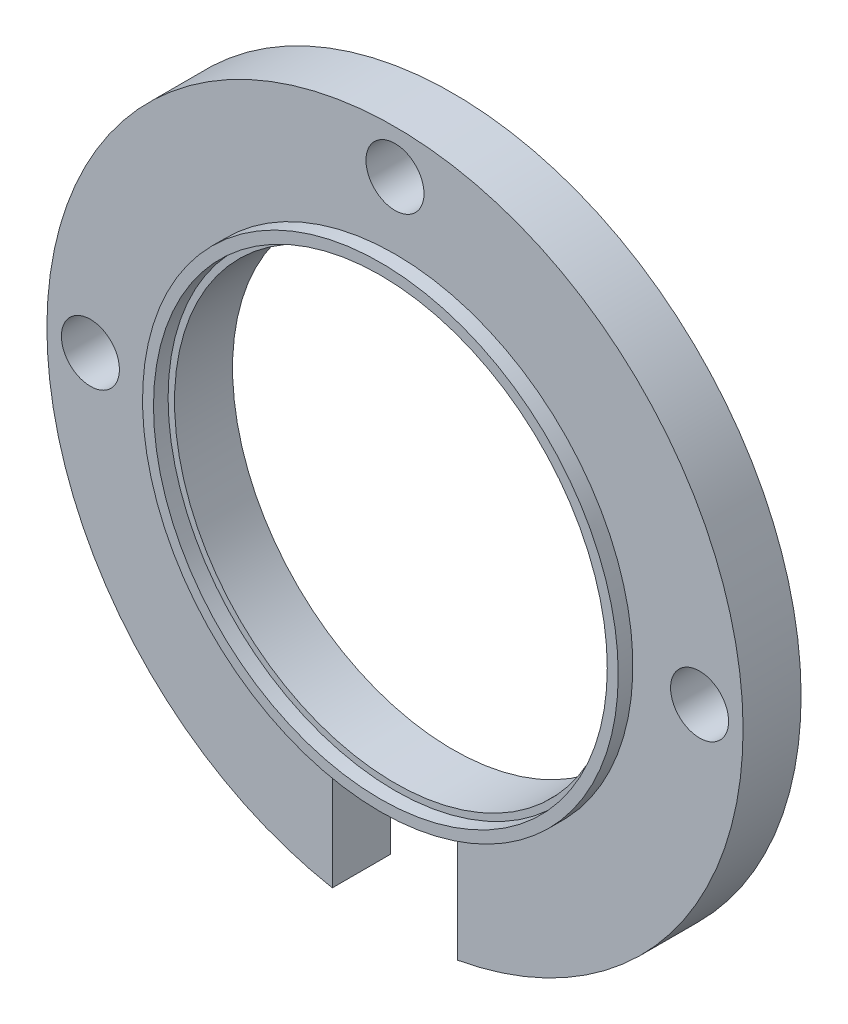
SolidWorks part; units mm, degrees
ref_plane "Front Plane" through (0, 0, 0) normal (0, 0, 1) x (1, 0, 0)
ref_plane "Top Plane" through (0, 0, 0) normal (0, 1, 0) x (1, 0, 0)
ref_plane "Right Plane" through (0, 0, 0) normal (1, 0, 0) x (0, 0, -1)
sketch "Sketch1" plane through (0, 0, 0) normal (0, 0, 1) x (1, 0, 0)
  circle A0 centre (0, 0) radius 19.05
  dimension "D1" = 38.1
extrude "Boss-Extrude1" add sketch "Sketch1" along normal blind 3.175
sketch "Sketch2" plane through (0, 0, 3.175) normal (0, 0, 1) x (1, 0, 0)
  circle A0 centre (0, 0) radius 12.065
  dimension "D1" = 24.13
extrude "Cut-Extrude1" cut sketch "Sketch2" against normal through all
sketch "Sketch3" plane through (0, 0, 3.175) normal (0, 0, 1) x (1, 0, 0)
  circle A0 centre (0, 0) radius 12.4175
  circle A1 centre (0, 0) radius 13.0175
  dimension "D1" = 26.035
  dimension "D2" = 0.6
extrude "Boss-Extrude2" add sketch "Sketch3" along normal blind 0.8
sketch "Sketch4" plane through (0, 0, 3.175) normal (0, 0, 1) x (1, 0, 0)
  line L1 (-3.429, -25.0825) -> (3.429, -25.0825)
  line L2 (-3.429, -25.0825) -> (-3.429, -13.0175)
  line L3 (-3.429, -13.0175) -> (3.429, -13.0175)
  line L4 (3.429, -25.0825) -> (3.429, -13.0175)
  line L5 (-3.429, -25.0825) -> (3.429, -13.0175) construction
  line L6 (-3.429, -13.0175) -> (3.429, -25.0825) construction
  circle A0 centre (0, 0) radius 19.05 construction
  circle A1 centre (0, 0) radius 13.0175 construction
  circle A2 centre (0, 0) radius 13.0175 construction
  point P0 (0, -19.05)
  point P7 (0, -13.0175)
  dimension "D1" = 6.858
extrude "Cut-Extrude2" cut sketch "Sketch4" against normal through all
sketch "Sketch5" plane through (0, 0, 0) normal (0, 0, -1) x (-1, 0, 0)
  circle A0 centre (0, 0) radius 16.6687 construction
  circle A1 centre (-16.6687, 0) radius 1.5875
  circle A2 centre (0, 16.6687) radius 1.5875
  circle A3 centre (16.6687, 0) radius 1.5875
  dimension "D1" = 33.3375
  dimension "D2" = 3.175
  dimension "D3" = 3.175
  dimension "D4" = 3.175
extrude "Cut-Extrude3" cut sketch "Sketch5" against normal through all
